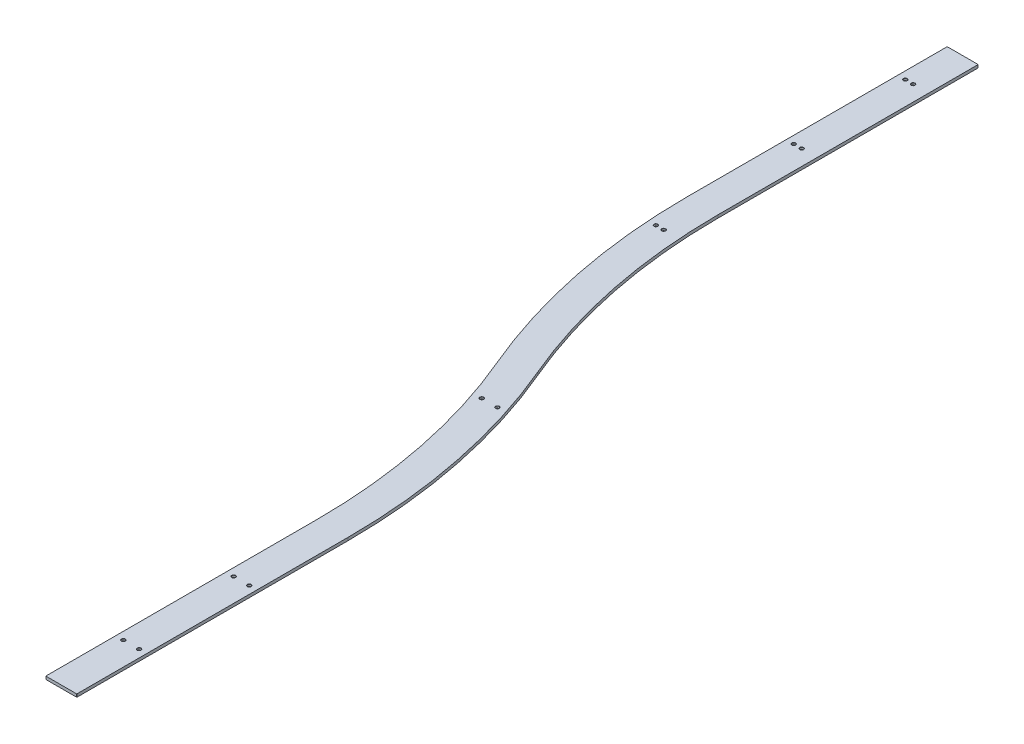
SolidWorks part; units mm, degrees
material "6061 Alloy"
ref_plane "Front" through (0, 0, 0) normal (0, 0, 1) x (1, 0, 0)
ref_plane "Top" through (0, 0, 0) normal (0, 1, 0) x (1, 0, 0)
ref_plane "Right" through (0, 0, 0) normal (1, 0, 0) x (0, 0, -1)
sketch "Sketch1" plane through (0, 0, 0) normal (0, 1, 0) x (1, 0, 0)
  line L0 (0, 74.1) -> (0, 950)
  line L1 (-304.8, 2450) -> (-304.8, 3290)
  line L2 (0, 0) -> (0, 74.1) construction
  arc A0 (0, 950) -> (-152.4, 1700) centre (-1921.6724, 950) ccw
  arc A1 (-304.8, 2450) -> (-152.4, 1700) centre (1616.8724, 2450) ccw
  dimension "D1" = 875.9
  dimension "D2" = 1500
  dimension "D3" = 840
  dimension "D4" = 304.8
  dimension "D5" = 74.1
extrude "Extrude-Thin1" add sketch "Sketch1" along normal blind 9.525 thin thin type mid plane wall 100
fillet "Fillet1" radius 1 4 edges at (-354.8, 4.7625, -3290) (-254.8, 4.7625, -3290) (50, 4.7625, -74.1) (-50, 4.7625, -74.1)
sketch "Sketch2" plane through (0, 9.525, 0) normal (0, 1, 0) x (1, 0, 0)
  line L0 (-304.8, 3130) -> (-304.8, 3104.6) construction
  line L1 (0, 0) -> (148.0994, 0) construction
  line L2 (-330.2, 3142.7) -> (-330.2, 3117.3)
  line L3 (-354.8, 3130) -> (-254.8, 3130)
  line L4 (-279.4, 3142.7) -> (-279.4, 3117.3)
  line L5 (-354.8, 2450) -> (-354.8, 3289) construction
  line L6 (-254.8, 2450) -> (-254.8, 3289) construction
  line L7 (-353.8, 3290) -> (-255.8, 3290) construction
  line L8 (-354.8, 2770) -> (-254.8, 2770) construction
  line L9 (-350.5096, 2320) -> (-250.2799, 2320) construction
  line L10 (-150.4772, 1555) -> (-45.1152, 1555) construction
  line L11 (-325.7947, 2320) -> (-274.9947, 2320)
  line L12 (-123.1962, 1555) -> (-72.3962, 1555)
  line L13 (-50, 656.05) -> (50, 656.05) construction
  line L14 (-50, 75.1) -> (-50, 950) construction
  line L15 (50, 75.1) -> (50, 950) construction
  line L16 (-25.4, 656.05) -> (25.4, 656.05)
  line L17 (-50, 300) -> (50, 300) construction
  line L18 (-25.4, 300) -> (25.4, 300)
  arc A3 (-354.8, 2450) -> (-198.4347, 1680.4857) centre (1616.8724, 2450) ccw construction
  arc A4 (-254.8, 2450) -> (-106.3653, 1719.5143) centre (1616.8724, 2450) ccw construction
  arc A5 (-50, 950) -> (-198.4347, 1680.4857) centre (-1921.6724, 950) ccw construction
  arc A6 (50, 950) -> (-106.3653, 1719.5143) centre (-1921.6724, 950) ccw construction
  point P17 (-279.4, 3130)
  point P18 (-279.4, 2770)
  point P19 (-330.2, 2770)
  point P41 (-97.7962, 1555)
  point P50 (0, 656.05)
  point P55 (0, 300)
  point P58 (-304.8, 2770)
  point P60 (-300.3947, 2320)
  dimension "D1" = 50.8
  dimension "D2" = 25.4
  dimension "D3" = 160
  dimension "D4" = 520
  dimension "D5" = 50.8
  dimension "D6" = 2633.95
  dimension "D7" = 970
  dimension "D8" = 1735
  dimension "D9" = 2990
hole_wizard "CBORE for 1/4 Socket Head Cap Screw3" positions "Sketch8" profile "Sketch7" counterbore size "1/4" standard "Ansi Inch" end condition through all
sketch "Sketch8" plane through (0, 9.525, 0) normal (0, 1, 0) x (-1, 0, 0)
  line L0 (354.8, -3130) -> (254.8, -3130) construction
  line L1 (330.2, -3142.7) -> (330.2, -3117.3) construction
  point P3 (304.8, -3130)
  point P6 (330.2, -3130)
  point P8 (304.8, -2770)
  point P11 (330.2, -2770)
  point P14 (300.3947, -2320)
  point P17 (325.7947, -2320)
  point P20 (72.3962, -1555)
  point P23 (123.1962, -1555)
  point P26 (-25.4, -656.05)
  point P29 (25.4, -656.05)
  point P32 (-25.4, -300)
  point P35 (25.4, -300)
sketch "Sketch7" plane through (-304.8, 9.525, -3130) normal (1, 0, 0) x (0, 0, 1)
  line L0 (0, 0) -> (0, 9.525)
  line L1 (3.3782, 8.89) -> (4.0132, 9.525)
  line L2 (5.5562, 6.35) -> (3.3782, 6.35)
  line L3 (3.3782, 6.35) -> (3.3782, 8.89)
  line L5 (5.5562, 6.35) -> (5.5562, 0.635)
  line L6 (5.5562, 0.635) -> (6.1913, 0)
  line L7 (6.1913, 0) -> (0, 0)
  line L8 (-5.5562, 0.635) -> (-6.1913, 0) construction
  line L11 (0, -6.35) -> (0, 107.95) construction
  line L12 (4.0132, 9.525) -> (0, 9.525)
  line L13 (-3.3782, 8.89) -> (-4.0132, 9.525) construction
  dimension "Thru Hole Dia." = 6.7564
  dimension "Thru Hole Depth" = 9.525
  dimension "C'Bore Dia." = 11.1125
  dimension "C'Bore Depth" = 6.35
  dimension "Near C'Sink Dia." = 12.3825
  dimension "Near C'Sink Angle" = 90
  dimension "Far C'Sink Dia." = 8.0264
  dimension "Far C'Sink Angle" = 90
mirror "Mirror1" [suppressed] about plane through (0, 0, 0) normal (1, 0, 0)
delete or keep bodies "Body-Delete1" [suppressed] type delete bodies bodies 104
